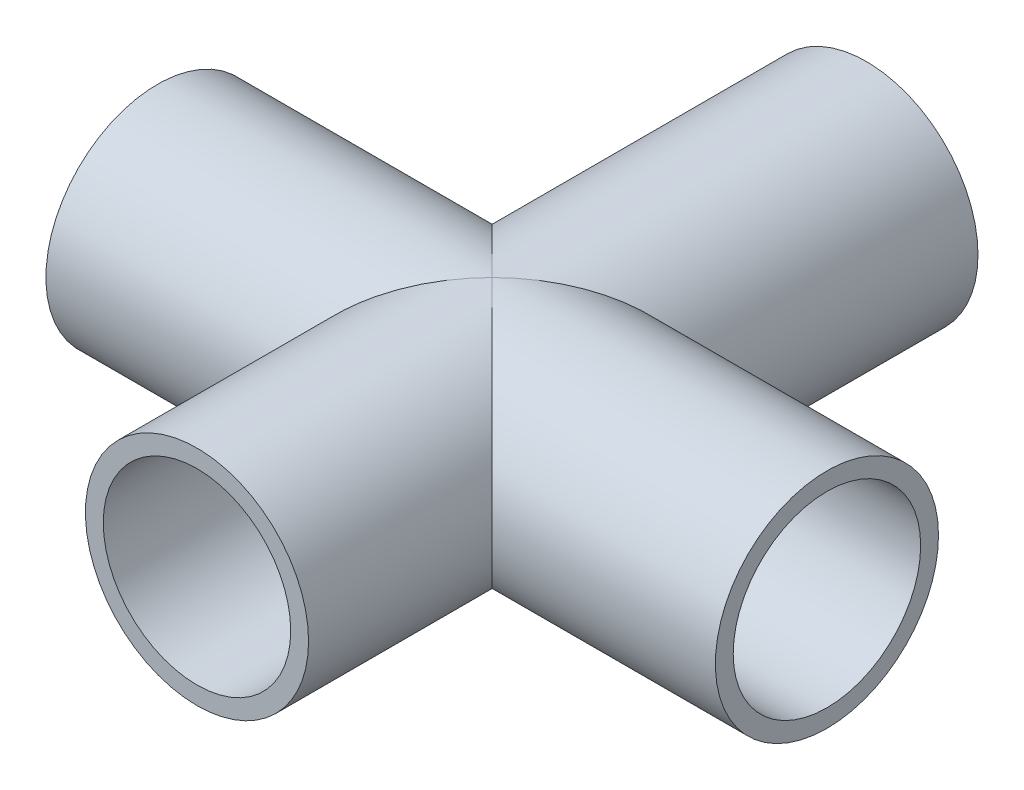
SolidWorks part; units mm, degrees
material "PVC Rigid"
ref_plane "Front Plane" through (0, 0, 0) normal (0, 0, 1) x (1, 0, 0)
ref_plane "Top Plane" through (0, 0, 0) normal (0, 1, 0) x (1, 0, 0)
ref_plane "Right Plane" through (0, 0, 0) normal (1, 0, 0) x (0, 0, -1)
sketch "Sketch1" plane through (0, 0, 0) normal (0, 0, 1) x (1, 0, 0)
  circle A1 centre (0, 0) radius 12.7
  circle A2 centre (0, 0) radius 10.668
  dimension "D1" = 25.4
  dimension "D2" = 21.336
extrude "Boss-Extrude1" add sketch "Sketch1" along normal blind 76.2
sketch "Sketch2" plane through (0, 0, 0) normal (1, 0, 0) x (0, 0, -1)
  line L3 (-85.1916, 0) -> (0, 0) construction
  line L4 (-85.1916, 20.955) -> (-85.1916, -20.955) construction
  circle A0 centre (-42.5958, 0) radius 12.7
  circle A1 centre (-42.5958, 0) radius 10.668
  dimension "D1" = 25.4
  dimension "D2" = 21.336
extrude "Boss-Extrude2" add sketch "Sketch2" along normal mid plane 76.2
